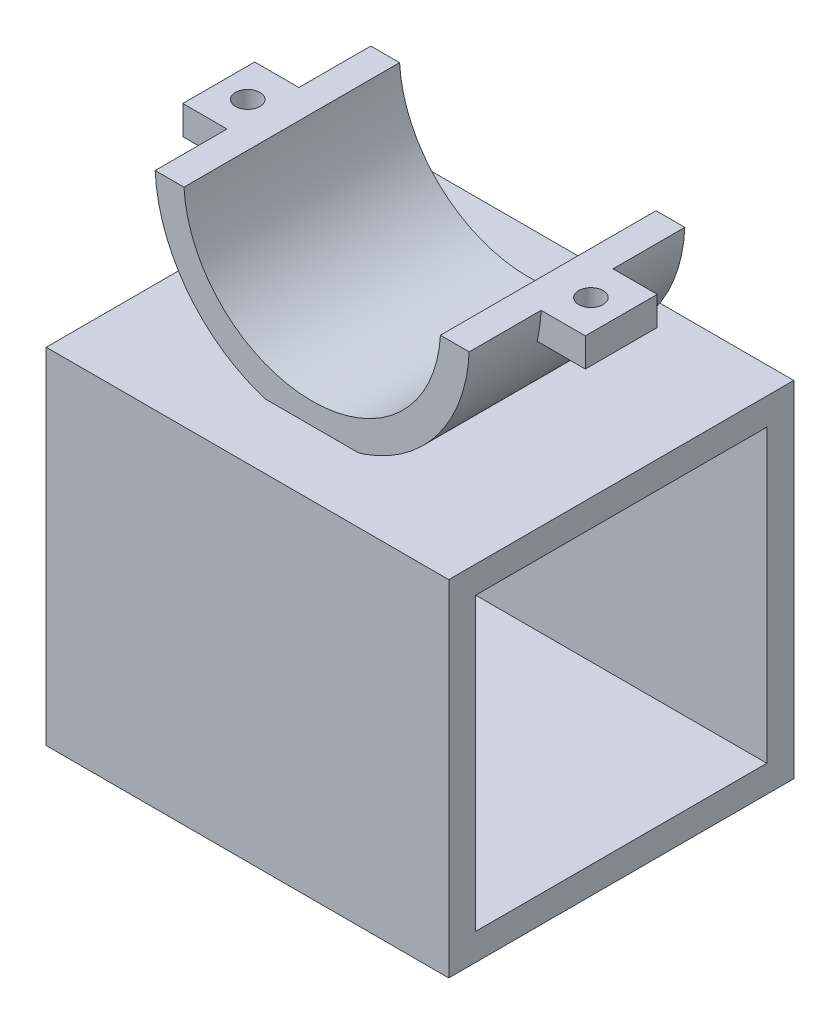
SolidWorks part; units mm, degrees
ref_plane "Front Plane" through (0, 0, 0) normal (0, 0, 1) x (1, 0, 0)
ref_plane "Top Plane" through (0, 0, 0) normal (0, 1, 0) x (1, 0, 0)
ref_plane "Right Plane" through (0, 0, 0) normal (1, 0, 0) x (0, 0, -1)
sketch "Sketch1" plane through (0, 0, 0) normal (0, 1, 0) x (1, 0, 0)
  line L0 (0, 19.621) -> (0, -19.621) construction
  line L2 (-21.87, 15) -> (-17.87, 15)
  line L3 (-21.87, 15) -> (-21.87, -15)
  line L4 (-21.87, -15) -> (-17.87, -15)
  line L5 (-17.87, 15) -> (-17.87, -15)
  line L6 (-21.87, 15) -> (-17.87, -15) construction
  line L7 (-21.87, -15) -> (-17.87, 15) construction
  point P0 (-19.87, 0)
  point P4 (0, 0)
  point P10 (-17.87, 0)
  dimension "D1" = 4
  dimension "D2" = 17.87
  dimension "D3" = 30
revolve "Revolve1" add sketch "Sketch1" angle 180 about L0
sketch "Sketch6" plane through (0, 0, 0) normal (0, 0, 1) x (1, 0, 0)
  line L0 (0, 0) -> (0, -14.1666) construction
  line L1 (-21.87, 0) -> (-17.87, 0) construction
  line L2 (-19.87, 0) -> (-28, 0)
  line L3 (-19.87, 0) -> (-19.87, -5)
  line L4 (-19.87, -5) -> (-28, -5)
  line L5 (-28, 0) -> (-28, -5)
  line L6 (19.87, -5) -> (28, -5)
  line L7 (28, 0) -> (28, -5)
  line L8 (19.87, 0) -> (28, 0)
  line L9 (19.87, 0) -> (19.87, -5)
  dimension "D1" = 8.13
  dimension "D2" = 5
extrude "Boss-Extrude3" add sketch "Sketch6" along normal blind 5 and the other way blind 5
hole_wizard "M3 Clearance Hole1" positions "Sketch7" profile "Sketch8" hole size "M3" standard "ISO"
sketch "Sketch7" plane through (0, 0, 0) normal (0, 1, 0) x (1, 0, 0)
  point P0 (-23.97, 0)
  point P3 (23.7783, 0)
sketch "Sketch8" plane through (-23.97, 0, 0) normal (1, 0, 0) x (0, 0, 1)
  line L0 (0, 0) -> (0, 9.8915)
  line L1 (0, 9.8915) -> (1.7, 8.87)
  line L2 (1.7, 8.87) -> (1.7, 0)
  line L5 (1.7, 0) -> (0, 0)
  line L10 (0, 9.8915) -> (-1.7, 8.87) construction
  line L11 (0, -6.35) -> (0, 107.95) construction
  dimension "Hole Dia." = 3.4
  dimension "Hole Depth" = 8.87
  dimension "Drill Angle" = 118
sketch "Sketch11" plane through (0, 0, 0) normal (0, 1, 0) x (1, 0, 0)
  line L1 (-31.0425, 20.9366) -> (31.0425, 20.9366)
  line L2 (-31.0425, 20.9366) -> (-31.0425, -20.9366)
  line L3 (-31.0425, -20.9366) -> (31.0425, -20.9366)
  line L4 (31.0425, 20.9366) -> (31.0425, -20.9366)
  line L5 (0, -20.9366) -> (0, 20.9366) construction
  line L6 (-31.0425, 0) -> (31.0425, 0) construction
  point P0 (0, 0)
extrude "Cut-Extrude1" cut sketch "Sketch11" against normal blind 1
sketch "Sketch4" plane through (0, 0, 0) normal (1, 0, 0) x (0, 0, -1)
  line L0 (-24, -20.87) -> (24, -20.87) construction
  line L2 (-20.25, -24.62) -> (20.25, -24.62)
  line L3 (-24, -20.87) -> (24, -20.87)
  line L4 (-24, -20.87) -> (-24, -68.87)
  line L5 (-24, -68.87) -> (24, -68.87)
  line L6 (24, -20.87) -> (24, -68.87)
  line L7 (-24, -20.87) -> (24, -68.87) construction
  line L8 (-24, -68.87) -> (24, -20.87) construction
  line L9 (-20.25, -24.62) -> (-20.25, -65.12)
  line L10 (-20.25, -65.12) -> (20.25, -65.12)
  line L11 (20.25, -24.62) -> (20.25, -65.12)
  line L12 (-20.25, -24.62) -> (20.25, -65.12) construction
  line L13 (-20.25, -65.12) -> (20.25, -24.62) construction
  point P0 (0, -44.87)
  point P3 (0, -20.87)
  point P9 (0, -20.87)
  point P10 (0, -44.87)
  dimension "D1" = 48
  dimension "D2" = 48
  dimension "D3" = 40.5
  dimension "D4" = 40.5
extrude "Boss-Extrude4" add sketch "Sketch4" along normal blind 28 and the other way blind 28 separate body
hole_wizard "M8 Clearance Hole1" positions "Sketch9" profile "Sketch10" hole size "M8" standard "ISO"
sketch "Sketch9" plane through (0, -65.12, 0) normal (0, 1, 0) x (1, 0, 0)
  point P0 (0, 0)
sketch "Sketch10" plane through (0, -65.12, 0) normal (1, 0, 0) x (0, 0, 1)
  line L0 (0, 0) -> (0, 11.5739)
  line L1 (0, 11.5739) -> (4.5, 8.87)
  line L2 (4.5, 8.87) -> (4.5, 0)
  line L5 (4.5, 0) -> (0, 0)
  line L10 (0, 11.5739) -> (-4.5, 8.87) construction
  line L11 (0, -6.35) -> (0, 107.95) construction
  dimension "Hole Dia." = 9
  dimension "Hole Depth" = 8.87
  dimension "Drill Angle" = 118
